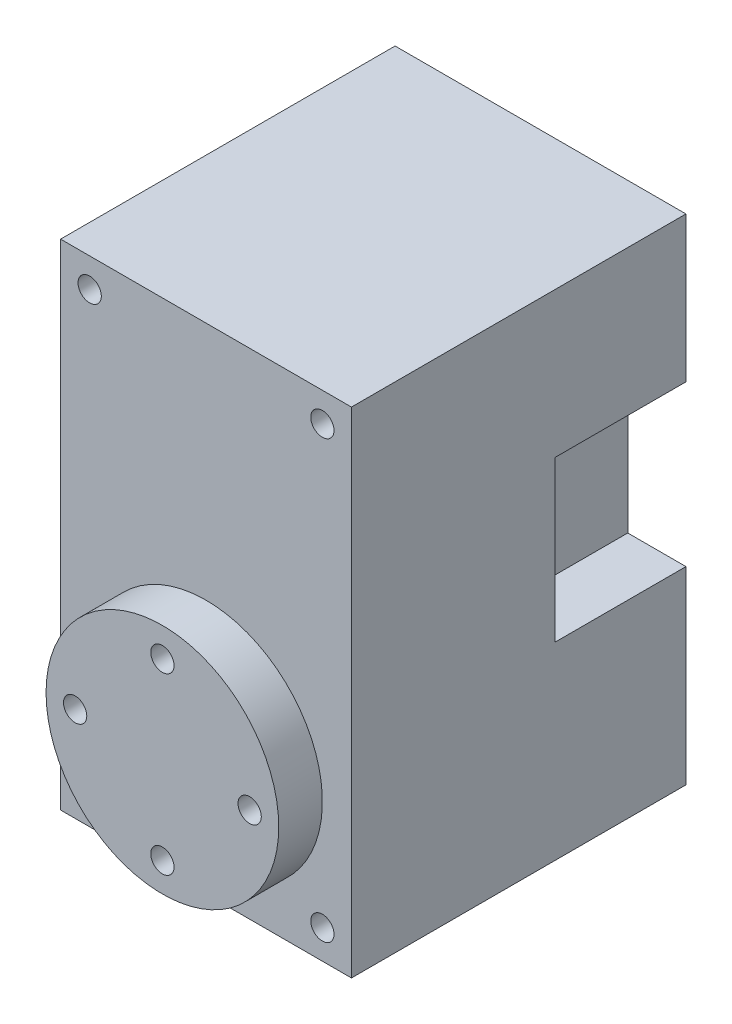
SolidWorks part; units mm, degrees
ref_plane "Front Plane" through (0, 0, 0) normal (0, 0, 1) x (1, 0, 0)
ref_plane "Top Plane" through (0, 0, 0) normal (0, 1, 0) x (1, 0, 0)
ref_plane "Right Plane" through (0, 0, 0) normal (1, 0, 0) x (0, 0, -1)
sketch "Sketch1" plane through (0, 0, 0) normal (0, 1, 0) x (1, 0, 0)
  line L1 (0, 0) -> (20, 0)
  line L2 (0, 0) -> (0, 23)
  line L3 (0, 23) -> (20, 23)
  line L4 (20, 0) -> (20, 23)
  dimension "D1" = 20
  dimension "D2" = 23
extrude "Boss-Extrude1" add sketch "Sketch1" along normal blind 34
sketch "Sketch2" plane through (0, 0, 0) normal (0, 0, 1) x (1, 0, 0)
  line L0 (10, 34) -> (10, 0) construction
  line L1 (0, 34) -> (20, 34) construction
  line L2 (0, 0) -> (20, 0) construction
  line L4 (2, 2) -> (18, 2) construction
  line L5 (2, 2) -> (2, 32) construction
  line L6 (2, 32) -> (18, 32) construction
  line L7 (18, 2) -> (18, 32) construction
  line L8 (2, 2) -> (18, 32) construction
  line L9 (2, 32) -> (18, 2) construction
  circle A0 centre (2, 32) radius 0.8
  circle A1 centre (18, 32) radius 0.8
  circle A2 centre (18, 2) radius 0.8
  circle A3 centre (2, 2) radius 0.8
  point P6 (10, 17)
  dimension "D3" = 1.6
  dimension "D1" = 30
  dimension "D2" = 16
extrude "Cut-Extrude1" cut sketch "Sketch2" against normal through all
sketch "Sketch3" plane through (0, 0, 0) normal (0, 0, 1) x (1, 0, 0)
  line L0 (10, 0) -> (10, 9.5) construction
  line L1 (0, 0) -> (20, 0) construction
  circle A0 centre (10, 9.5) radius 8
  circle A1 centre (10, 9.5) radius 6 construction
  circle A2 centre (10, 15.5) radius 0.8
  circle A3 centre (4, 9.5) radius 0.8
  circle A4 centre (10, 3.5) radius 0.8
  circle A5 centre (16, 9.5) radius 0.8
  dimension "D2" = 16
  dimension "D3" = 1.6
  dimension "D4" = 12
  dimension "D1" = 9.5
extrude "Boss-Extrude2" add sketch "Sketch3" along normal blind 3
sketch "Sketch4" plane through (0, 0, -23) normal (0, 0, -1) x (-1, 0, 0)
  line L0 (-20, 34) -> (-20, 0) construction
  line L1 (-20, 13) -> (-16, 13)
  line L2 (-20, 13) -> (-20, 24)
  line L3 (-20, 24) -> (-16, 24)
  line L4 (-16, 13) -> (-16, 24)
  line L5 (0, 34) -> (0, 0) construction
  line L6 (0, 13) -> (-4, 13)
  line L7 (0, 13) -> (0, 24)
  line L8 (0, 24) -> (-4, 24)
  line L9 (-4, 13) -> (-4, 24)
  dimension "D1" = 10
  dimension "D2" = 11
  dimension "D3" = 4
extrude "Cut-Extrude2" cut sketch "Sketch4" against normal blind 9
